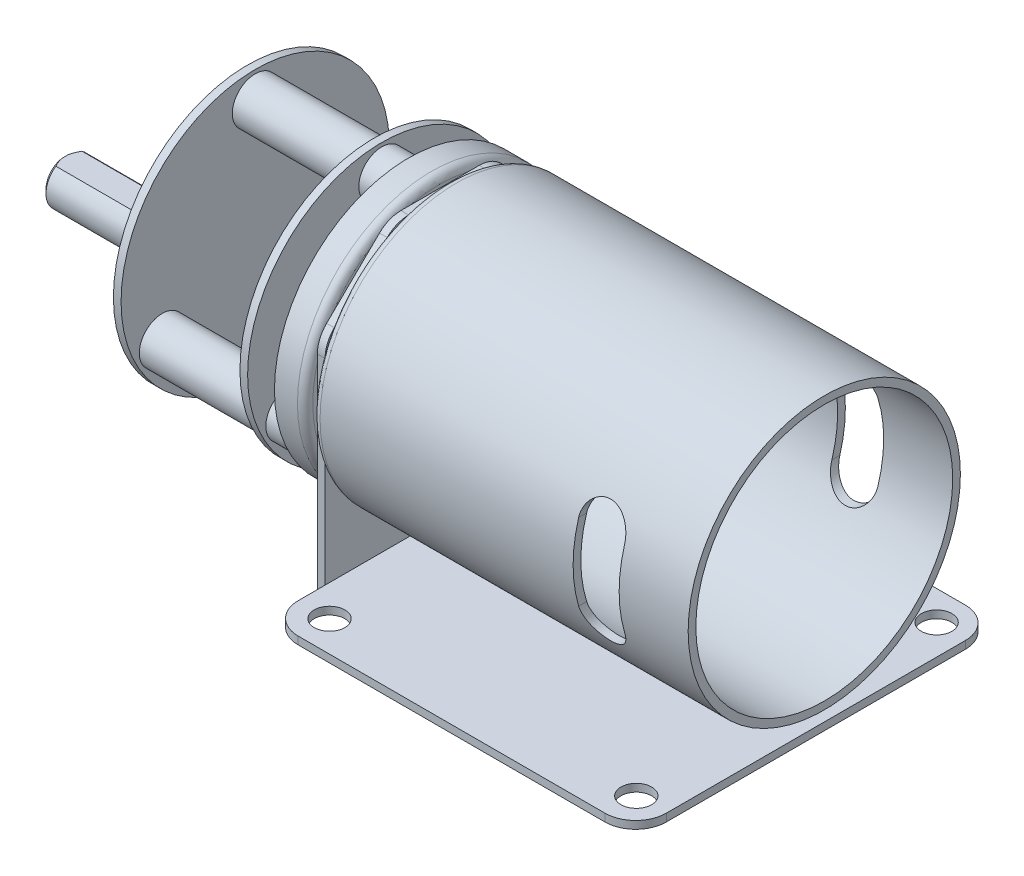
SolidWorks part; units mm, degrees
ref_plane "Front Plane" through (0, 0, 0) normal (0, 0, 1) x (1, 0, 0)
ref_plane "Top Plane" through (0, 0, 0) normal (0, 1, 0) x (1, 0, 0)
ref_plane "Right Plane" through (0, 0, 0) normal (1, 0, 0) x (0, 0, -1)
sketch "Sketch1" plane through (0, 0, 0) normal (0, 1, 0) x (1, 0, 0)
  line L0 (-24, -23.5) -> (24, 23.5) construction
  line L1 (-20, 23.5) -> (20, 23.5)
  line L2 (-24, 19.5) -> (-24, -19.5)
  line L3 (-20, -23.5) -> (20, -23.5)
  line L4 (24, 19.5) -> (24, -19.5)
  line L5 (-24, 23.5) -> (24, -23.5) construction
  circle A0 centre (-19.9149, 19.5) radius 2
  circle A1 centre (20.0851, 19.6667) radius 2
  circle A2 centre (-19.9149, -19.5) radius 2
  circle A3 centre (20.0851, -19.5) radius 2
  arc A4 (-24, 19.5) -> (-20, 23.5) centre (-20, 19.5) cw
  arc A5 (-20, -23.5) -> (-24, -19.5) centre (-20, -19.5) cw
  arc A6 (20, -23.5) -> (24, -19.5) centre (20, -19.5) ccw
  arc A7 (20, 23.5) -> (24, 19.5) centre (20, 19.5) cw
  point P4 (0, 0)
  dimension "D3" = 4
  dimension "D4" = 4
  dimension "D5" = 4
  dimension "D6" = 4
  dimension "D9" = 4
  dimension "D1" = 48
  dimension "D2" = 47
  dimension "D7" = 39
  dimension "D8" = 40
extrude "Extrude1" add sketch "Sketch1" along normal blind 1
sketch "Sketch2" plane through (0, 0, 0) normal (0, -1, 0) x (1, 0, 0)
  line L0 (-24, -19.5) -> (-24, 19.5) construction
  line L1 (-25, 16) -> (-24, 16)
  line L2 (-25, 16) -> (-25, -16)
  line L3 (-25, -16) -> (-24, -16)
  line L4 (-24, 16) -> (-24, -16)
  point P4 (-24, 0)
  dimension "D1" = 32
  dimension "D2" = 1
extrude "Extrude2" add sketch "Sketch2" against normal blind 38
sketch "Sketch3" plane through (-24, 0, 0) normal (1, 0, 0) x (0, 0, -1)
  circle A0 centre (0, 21.2) radius 12.5
  dimension "D1" = 25
  dimension "D2" = 21.2
extrude "Extrude3" add sketch "Sketch3" along normal blind 0.1 and the other way blind 1.1
sketch "Sketch4" plane through (-23.9, 0, 0) normal (1, 0, 0) x (0, 0, -1)
  circle A0 centre (0, 21.2) radius 17.75
  circle A1 centre (0, 21.2) radius 12.5 construction
  dimension "D1" = 35.5
extrude "Extrude4" add sketch "Sketch4" along normal blind 1
sketch "Sketch5" plane through (-22.9, 0, 0) normal (1, 0, 0) x (0, 0, -1)
  circle A0 centre (0, 21.2) radius 17.75 construction
  circle A1 centre (0, 21.2) radius 17.75
  circle A2 centre (0, 21.2) radius 16.75
  dimension "D1" = 1
extrude "Extrude5" add sketch "Sketch5" along normal blind 48
sketch "Sketch6" plane through (0, 0, 0) normal (0, 0, 1) x (1, 0, 0)
  line L0 (25.1, 3.45) -> (25.1, 38.95) construction
  line L2 (10.1, 26.2) -> (10.1, 16.2)
  line L4 (16.1, 26.2) -> (16.1, 16.2)
  line L7 (-12.3236, 21.2) -> (2.2598, 21.2) construction
  arc A0 (16.1, 26.2) -> (10.1, 26.2) centre (13.1, 26.2) ccw
  arc A1 (16.1, 16.2) -> (10.1, 16.2) centre (13.1, 16.2) cw
  point P6 (10.1, 21.2)
  dimension "D5" = 3
  dimension "D6" = 3
  dimension "D1" = 10
  dimension "D3" = 9
  dimension "D4" = 21.2
extrude "Cut-Extrude1" cut sketch "Sketch6" against normal blind 48 and the other way blind 48
sketch "Sketch7" plane through (-25.1, 0, 0) normal (-1, 0, 0) x (0, 0, 1)
  circle A0 centre (0, 21.2) radius 17.5
  circle A1 centre (0, 21.2) radius 12.5 construction
  dimension "D1" = 35
extrude "Extrude6" add sketch "Sketch7" along normal blind 4
sketch "Sketch8" plane through (-29.1, 0, 0) normal (-1, 0, 0) x (0, 0, 1)
  line L0 (0, 35.2) -> (12.1244, 14.2) construction
  line L1 (12.1244, 14.2) -> (-12.1244, 14.2) construction
  line L2 (-12.1244, 14.2) -> (0, 35.2) construction
  circle A0 centre (0, 35.2) radius 3
  circle A1 centre (12.1244, 14.2) radius 3
  circle A2 centre (-12.1244, 14.2) radius 3
  circle A3 centre (0, 21.2) radius 17.5 construction
  dimension "D1" = 6
  dimension "D2" = 6
  dimension "D3" = 6
  dimension "D4" = 14
  dimension "D5" = 14
extrude "Extrude7" add sketch "Sketch8" along normal blind 21
sketch "Sketch9" plane through (-50.1, 0, 0) normal (-1, 0, 0) x (0, 0, 1)
  circle A0 centre (0, 21.2) radius 17.5 construction
  circle A1 centre (0, 21.2) radius 17.5
extrude "Extrude8" add sketch "Sketch9" against normal blind 1
fillet "Fillet1" radius 1 3 edges at (-23.9, 21.2, -17.75) (-22.9, 21.2, -16.75) (-25.1, 21.2, 17.5)
sketch "Sketch10" plane through (-50.1, 0, 0) normal (-1, 0, 0) x (0, 0, 1)
  circle A0 centre (0, 14) radius 6
  dimension "D1" = 12
  dimension "D2" = 14
ref_plane "Plane1" through (-58.9, 0, 0) normal (1, 0, 0) x (0, 0, -1)
extrude "Extrude9" add sketch "Sketch10" along normal up to surface (8.8 mm away) up to plane "Plane1"
sketch "Sketch12" plane through (-58.9, 0, 0) normal (-1, 0, 0) x (0, 0, 1)
  circle A0 centre (0, 14) radius 2.99
  dimension "D1" = 5.98
extrude "Extrude10" add sketch "Sketch12" along normal blind 15
chamfer "Chamfer1" distance 0.5 angle 45 2 edges at (-58.9, 14, -6) (-73.9, 14, 2.99)
sketch "Sketch13" plane through (-73.9, 0, 0) normal (-1, 0, 0) x (0, 0, 1)
  line L1 (-4.2541, 20.1255) -> (4.568, 20.1255)
  line L2 (-4.2541, 20.1255) -> (-4.2541, 16.46)
  line L3 (-4.2541, 16.46) -> (4.568, 16.46)
  line L4 (4.568, 20.1255) -> (4.568, 16.46)
  circle A0 centre (0, 14) radius 2.99 construction
  dimension "D1" = 2.46
extrude "Cut-Extrude2" cut sketch "Sketch13" against normal blind 12
ref_plane "Plane2" through (-32.6, 0, 0) normal (-1, 0, 0) x (0, 0, 1)
sketch "Sketch14" plane through (-32.6, 0, 0) normal (-1, 0, 0) x (0, 0, 1)
  circle A0 centre (0, 21.2) radius 17.5 construction
  circle A1 centre (0, 21.2) radius 17.5
extrude "Extrude11" add sketch "Sketch14" along normal blind 1
sketch "Sketch15" plane through (-25, 0, 0) normal (-1, 0, 0) x (0, 0, 1)
  line L0 (-33.8742, 26.3127) -> (-16, 20.1196)
  line L2 (-16, 20.1196) -> (-16, 26.6059)
  line L3 (-5.1023, 37.3528) -> (5.1023, 37.3528)
  line L4 (-16, 38) -> (-16, 0) construction
  line L5 (-14.797, 29.4654) -> (-7.8993, 36.2123)
  line L6 (28.6479, 26.3127) -> (28.6479, 45.5361)
  line L7 (28.6479, 45.5361) -> (-33.8742, 45.5361)
  line L8 (-33.8742, 45.5361) -> (-33.8742, 26.3127)
  line L9 (16, 20.1196) -> (16, 26.6059)
  line L10 (28.6479, 26.3127) -> (16, 20.1196)
  line L11 (16, 38) -> (16, 0) construction
  line L12 (14.797, 29.4654) -> (7.8993, 36.2123)
  circle A0 centre (0, 21.2) radius 17.5 construction
  arc A1 (-14.797, 29.4654) -> (-16, 26.6059) centre (-12, 26.6059) ccw
  arc A2 (-5.1023, 37.3528) -> (-7.8993, 36.2123) centre (-5.1023, 33.3528) ccw
  arc A3 (7.8993, 36.2123) -> (5.1023, 37.3528) centre (5.1023, 33.3528) ccw
  arc A4 (16, 26.6059) -> (14.797, 29.4654) centre (12, 26.6059) ccw
  point P18 (-16, 28.2887)
  point P21 (-6.7333, 37.3528)
  point P24 (6.7333, 37.3528)
  point P27 (16, 28.2887)
  dimension "D1" = 4
extrude "Cut-Extrude3" cut sketch "Sketch15" against normal blind 1
